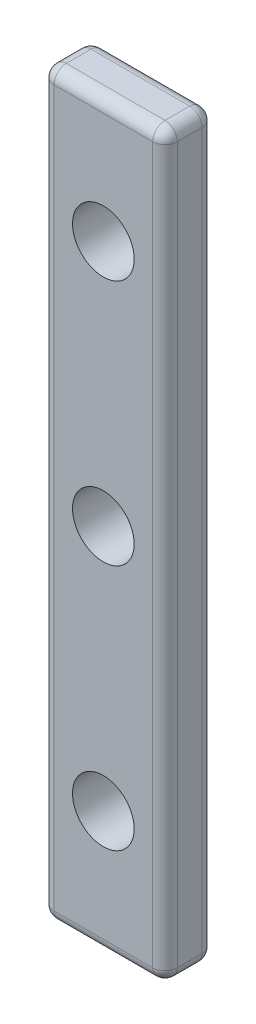
SolidWorks part; units mm, degrees
ref_plane "Front Plane" through (0, 0, 0) normal (0, 0, 1) x (1, 0, 0)
ref_plane "Top Plane" through (0, 0, 0) normal (0, 1, 0) x (1, 0, 0)
ref_plane "Right Plane" through (0, 0, 0) normal (1, 0, 0) x (0, 0, -1)
sketch "Sketch2" plane through (0, 0, 0) normal (0, 0, 1) x (1, 0, 0)
  line L1 (0, 0) -> (10, 0)
  line L2 (0, 0) -> (0, 60)
  line L3 (0, 60) -> (10, 60)
  line L4 (10, 0) -> (10, 60)
  circle A0 centre (5, 50) radius 2.5
  circle A1 centre (5, 10) radius 2.5
  circle A2 centre (5, 30) radius 2.5
extrude "Boss-Extrude1" add sketch "Sketch2" along normal blind 4
fillet "Fillet1" radius 1 12 edges at (5, 60, 0) (10, 30, 0) (0, 30, 0) (5, 0, 0) (5, 0, 4) (10, 30, 4) (0, 30, 4) (5, 60, 4) (0, 0, 2) (10, 0, 2) (10, 60, 2) (0, 60, 2)
